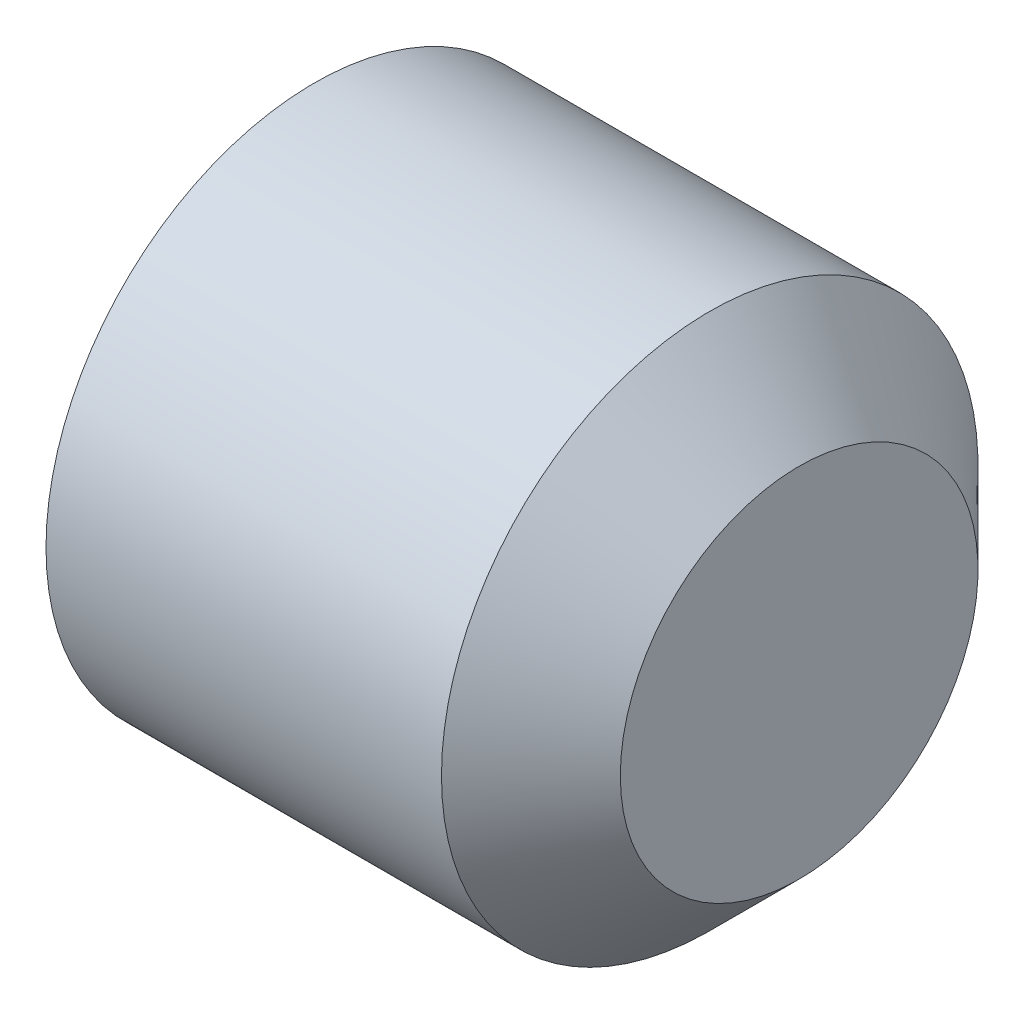
SolidWorks part; units mm, degrees
ref_plane "Спереди" through (0, 0, 0) normal (0, 0, 1) x (1, 0, 0)
ref_plane "Сверху" through (0, 0, 0) normal (0, 1, 0) x (1, 0, 0)
ref_plane "Справа" through (0, 0, 0) normal (1, 0, 0) x (0, 0, -1)
ref_plane "Плоскость1" through (0, 0, 0) normal (0, 0, -1) x (-1, 0, 0)
sketch "Эскиз1" plane through (0, 0, 0) normal (0, 0, -1) x (-1, 0, 0)
  line L0 (-6, 2) -> (-6, 0)
  line L1 (-6, 0) -> (0, 0)
  line L2 (0, 0) -> (0, 3)
  line L3 (0, 3) -> (-5, 3)
  line L4 (-5, 3) -> (-6, 2)
  line L6 (-6, 0) -> (0, 0) construction
  dimension "D1" = 3
  dimension "D2" = 6
  dimension "D3" = 45
  dimension "D4" = 2
revolve "Повернуть1" add sketch "Эскиз1" angle 360 about L6
sketch "Эскиз2" plane through (0, 0, 0) normal (-1, 0, 0) x (0, 0, 1)
  line L0 (1.7321, 0) -> (0.866, 1.5)
  line L1 (0.866, 1.5) -> (-0.866, 1.5)
  line L2 (-0.866, 1.5) -> (-1.7321, 0)
  line L3 (-1.7321, 0) -> (-0.866, -1.5)
  line L4 (-0.866, -1.5) -> (0.866, -1.5)
  line L5 (0.866, -1.5) -> (1.7321, 0)
extrude "Вырез-Вытянуть1" cut sketch "Эскиз2" against normal blind 2
chamfer "Фаска1" distance 1 angle 30 1 edges at (0, 0, 3)
fillet "Скругление1" radius 0.1 13 edges at (2, -1.5, 0) (2, -0.75, -1.299) (2, 0.75, -1.299) (2, 1.5, 0) (2, 0.75, 1.299) (2, -0.75, 1.299) (0, 0.75, 1.299) (0, 1.5, 0) (0, 0.75, -1.299) (0, -0.75, -1.299) (0, -1.5, 0) (0, -0.75, 1.299) (0, 0, 2)
